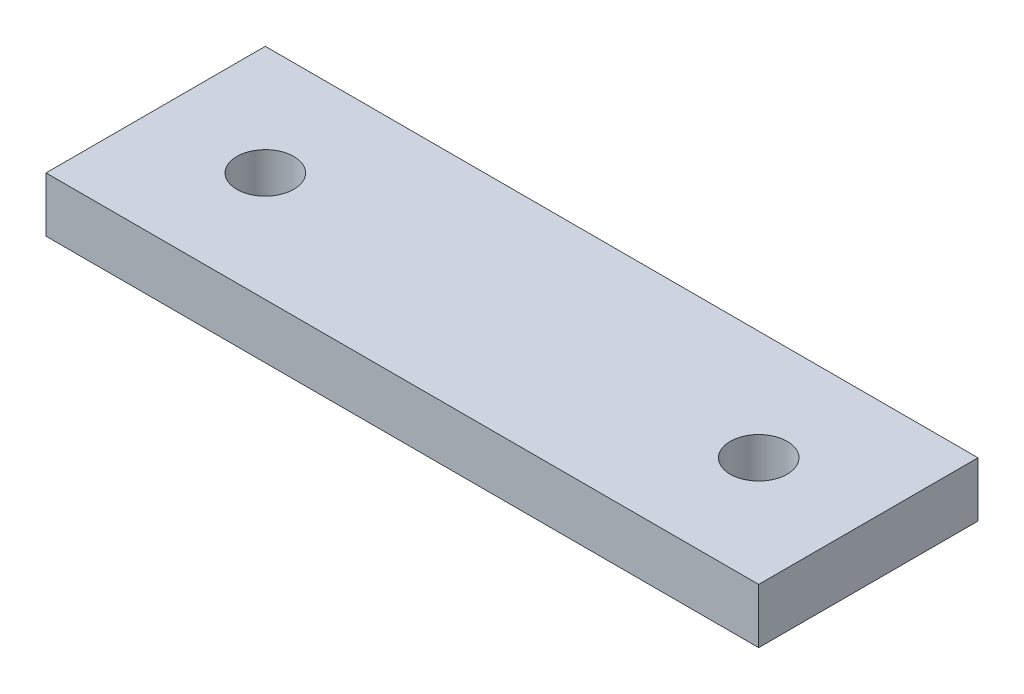
SolidWorks part; units mm, degrees
ref_plane "Front Plane" through (0, 0, 0) normal (0, 0, 1) x (1, 0, 0)
ref_plane "Top Plane" through (0, 0, 0) normal (0, 1, 0) x (1, 0, 0)
ref_plane "Right Plane" through (0, 0, 0) normal (1, 0, 0) x (0, 0, -1)
sketch "Sketch1" plane through (0, 0, 0) normal (0, 1, 0) x (1, 0, 0)
  line L0 (0, 12.7) -> (82.55, 12.7) construction
  line L1 (0, 0) -> (82.55, 0)
  line L2 (0, 0) -> (0, 25.4)
  line L3 (0, 25.4) -> (82.55, 25.4)
  line L4 (82.55, 0) -> (82.55, 25.4)
  circle A0 centre (12.7, 12.7) radius 3.302
  circle A1 centre (69.85, 12.7) radius 3.302
  point P11 (12.7, 12.7)
  dimension "D4" = 6.604
  dimension "D1" = 82.55
  dimension "D5" = 25.4
  dimension "D2" = 57.15
  dimension "D3" = 12.7
extrude "Boss-Extrude1" add sketch "Sketch1" along normal blind 6.35
equation "\"width\"= \"D1@Sketch1\""
equation "\"D3@Sketch1\"=(\"width\"-\"D2@Sketch1\")/2"
